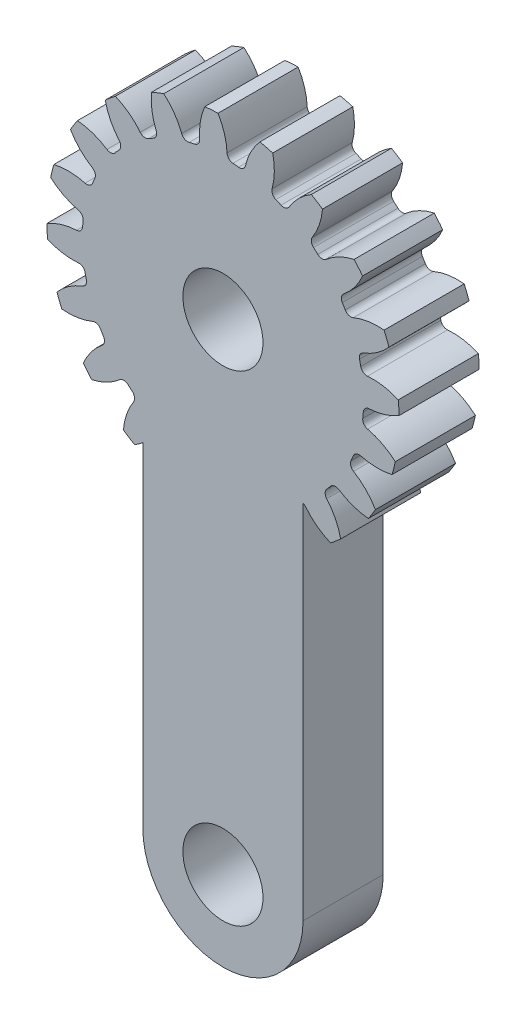
SolidWorks part; units mm, degrees
material "ABS"
ref_plane "Front" through (0, 0, 0) normal (0, 0, 1) x (1, 0, 0)
ref_plane "Top" through (0, 0, 0) normal (0, 1, 0) x (1, 0, 0)
ref_plane "Right" through (0, 0, 0) normal (1, 0, 0) x (0, 0, -1)
sketch "Sketch3" plane through (0, 0, 0) normal (0, 0, 1) x (1, 0, 0)
  circle A0 centre (0, 0) radius 27.94
  dimension "od" = 55.88
extrude "gearBody" add sketch "Sketch3" along normal blind 12.7
sketch "Sketch2" plane through (0, 0, 0) normal (0, 0, 1) x (1, 0, 0)
  line L0 (0, 0) -> (22.7191, 9.4105) construction
  line L1 (29.8471, -9.3212) -> (0, 0) construction
  line L2 (0, 0) -> (36.3143, 0) construction
  line L3 (25.3982, -0.3053) -> (25.0293, -4.3236) construction
  line L5 (25.2137, -2.3145) -> (0, 0) construction
  line L7 (0, 0) -> (24.591, 0) construction
  arc A0 (24.586, -0.4935) -> (24.265, -3.9907) centre (0, 0) ccw construction
  arc A1 (27.929, 0.7831) -> (27.3197, -5.8547) centre (0, 0) ccw construction
  arc A2 (25.3982, -0.3053) -> (25.0293, -4.3236) centre (0, 0) ccw construction
  arc A3 (22.162, -2.4879) -> (22.2446, -1.5884) centre (0, 0) ccw
  arc A4 (29.8471, -9.3212) -> (22.9306, -3.5779) centre (20.6262, -13.3894) ccw
  arc A5 (29.8471, -9.3212) -> (31.0453, 3.7316) centre (0, 0) ccw
  arc A6 (31.0453, 3.7316) -> (23.1988, -0.6565) centre (22.7191, 9.4105) cw
  arc A7 (22.2446, -1.5884) -> (23.1988, -0.6565) centre (23.2466, -1.66) cw
  arc A8 (22.9306, -3.5779) -> (22.162, -2.4879) centre (23.1603, -2.5999) cw
  point P6 (31.0453, 3.7316)
  point P22 (29.8471, -9.3212)
  dimension "baseDia" = 49.1819
  dimension "od" = 55.88
  dimension "pd" = 50.8
  dimension "rd" = 44.6024
  dimension "rFillet" = 1.0046
  dimension "pointX" = 31.0453
  dimension "pointY" = 3.7316
  dimension "CTT" = 4.0183
  dimension "flankCenterAngle" = 22.5
extrude "toothCut" cut sketch "Sketch2" along normal through all
pattern_circular "CirPattern1" count 20 over 360 about axis through (0, 0, 0) along (0, 0, 1) of "toothCut"
sketch "boreDia" plane through (0, 0, 0) normal (0, 0, 1) x (1, 0, 0)
  circle A0 centre (0, 0) radius 6.35
  dimension "boreDia" = 12.7
extrude "bore" cut sketch "boreDia" against normal mid plane 25400
sketch3d "3DSketch1" plane through (0, 0, 0) normal (0, 0, 1) x (1, 0, 0)
sketch "Sketch4" plane through (0, 0, 0) normal (0, 0, 1) x (1, 0, 0)
  line L0 (0, 0) -> (0, -76.2) construction
  line L1 (-12.7, -18.3318) -> (-12.7, -76.2)
  line L2 (12.7, -18.3318) -> (12.7, -76.2)
  line L3 (-12.7, -76.2) -> (12.7, -76.2) construction
  circle A0 centre (0, 0) radius 22.3012 construction
  arc A1 (-9.2145, -20.3085) -> (-8.3846, -20.665) centre (0, 0) ccw construction
  circle A2 centre (0, -76.2) radius 6.35
  arc A3 (-12.7, -76.2) -> (12.7, -76.2) centre (0, -76.2) ccw
  arc A4 (-12.7, -18.3318) -> (12.7, -18.3318) centre (0, 0) ccw
  point P11 (0, -76.2)
  dimension "D3" = 12.7
  dimension "D1" = 25.4
  dimension "D2" = 76.2
extrude "Boss-Extrude1" add sketch "Sketch4" along normal blind 12.7
